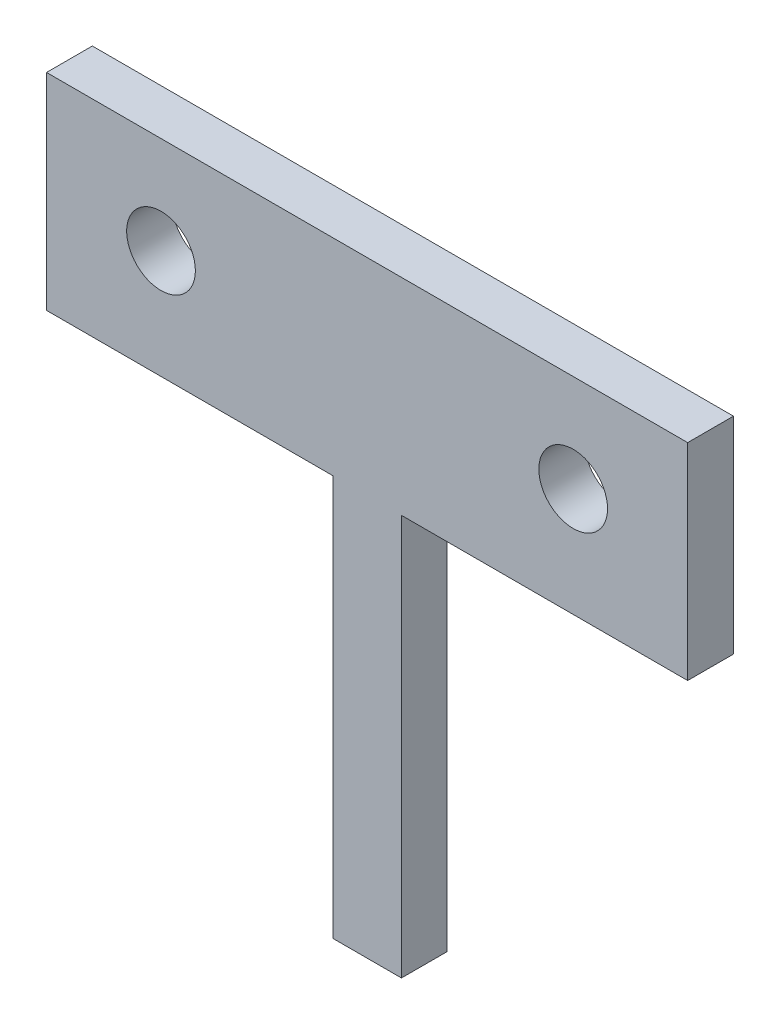
SolidWorks part; units mm, degrees
ref_plane "Front Plane" through (0, 0, 0) normal (0, 0, 1) x (1, 0, 0)
ref_plane "Top Plane" through (0, 0, 0) normal (0, 1, 0) x (1, 0, 0)
ref_plane "Right Plane" through (0, 0, 0) normal (1, 0, 0) x (0, 0, -1)
sketch "Sketch1" plane through (0, 0, 0) normal (0, 0, 1) x (1, 0, 0)
  line L0 (5, 4.75) -> (23, 4.75) construction
  line L1 (0, 0) -> (28, 0)
  line L2 (0, 0) -> (0, 9)
  line L3 (0, 9) -> (28, 9)
  line L4 (28, 0) -> (28, 9)
  line L5 (12.5, 0) -> (15.5, 0)
  line L6 (12.5, 0) -> (12.5, -17.5)
  line L7 (12.5, -17.5) -> (15.5, -17.5)
  line L8 (15.5, 0) -> (15.5, -17.5)
  circle A0 centre (5, 4.75) radius 1.5
  circle A1 centre (23, 4.75) radius 1.5
  point P9 (14, 0)
  point P15 (5, 4.75)
  point P16 (23, 4.75)
  point P19 (14, 4.75)
  point P20 (14, 9)
  dimension "D9" = 3
  dimension "D1" = 28
  dimension "D2" = 9
  dimension "D3" = 3
  dimension "D4" = 17.5
  dimension "D7" = 4.25
  dimension "D8" = 18
extrude "Boss-Extrude1" add sketch "Sketch1" along normal blind 2
